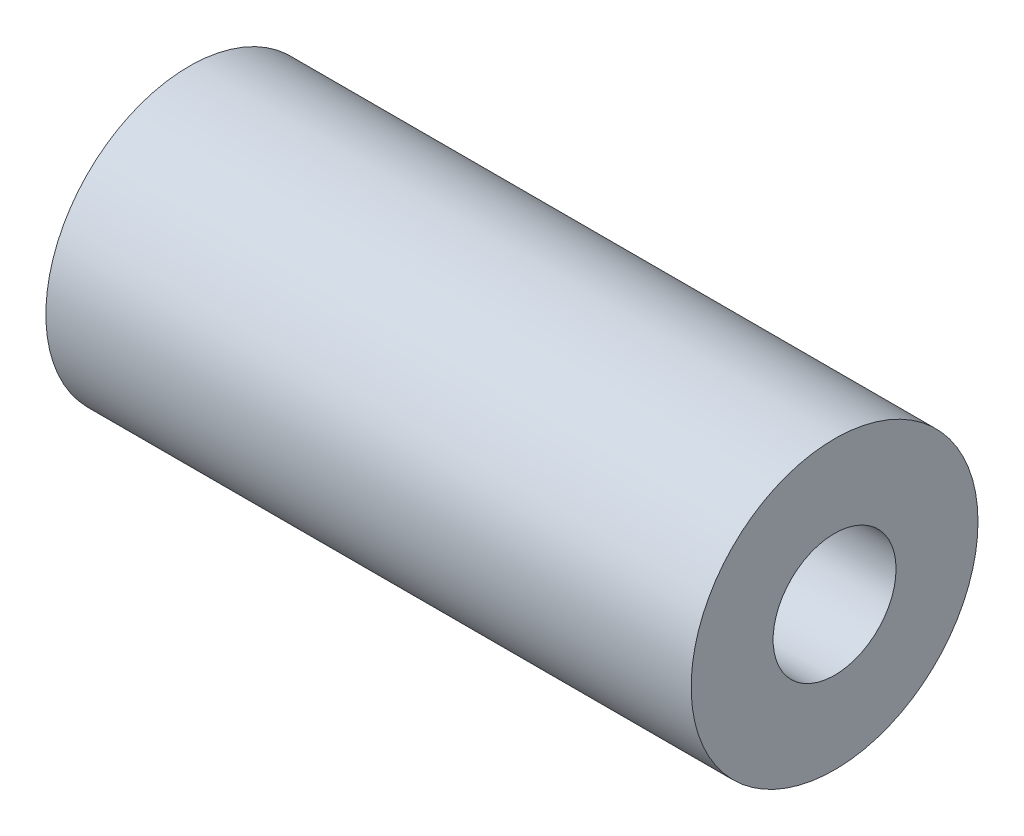
SolidWorks part; units mm, degrees
material "NEOPRENE"
ref_plane "Front Plane" through (0, 0, 0) normal (0, 0, 1) x (1, 0, 0)
ref_plane "Top Plane" through (0, 0, 0) normal (0, 1, 0) x (1, 0, 0)
ref_plane "Right Plane" through (0, 0, 0) normal (1, 0, 0) x (0, 0, -1)
sketch "Sketch1" plane through (0, 0, 0) normal (1, 0, 0) x (0, 0, -1)
  circle A0 centre (0, 0) radius 11.1125
  circle A1 centre (0, 0) radius 4.7625
  dimension "D1" = 22.225
  dimension "D2" = 9.525
extrude "Boss-Extrude1" add sketch "Sketch1" along normal mid plane 50
